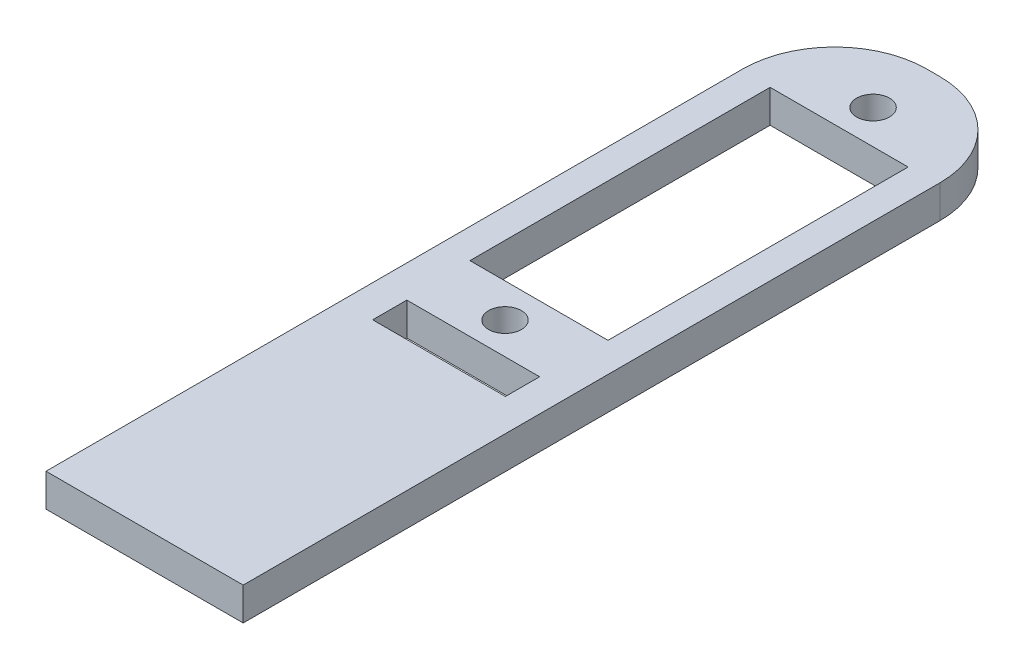
SolidWorks part; units mm, degrees
ref_plane "Front Plane" through (0, 0, 0) normal (0, 0, 1) x (1, 0, 0)
ref_plane "Top Plane" through (0, 0, 0) normal (0, 1, 0) x (1, 0, 0)
ref_plane "Right Plane" through (0, 0, 0) normal (1, 0, 0) x (0, 0, -1)
sketch "Sketch1" plane through (0, 0, 0) normal (0, 1, 0) x (1, 0, 0)
  line L0 (0, 29) -> (0, 0) construction
  line L1 (-9.525, 38.1) -> (9.525, 38.1)
  line L2 (-9.525, 38.1) -> (-9.525, -38.1)
  line L3 (-9.525, -38.1) -> (9.525, -38.1)
  line L4 (9.525, 38.1) -> (9.525, -38.1)
  line L5 (-6.6675, 29) -> (6.6675, 29)
  line L6 (-6.6675, 29) -> (-6.6675, 0)
  line L7 (-6.6675, 0) -> (6.6675, 0)
  line L8 (6.6675, 29) -> (6.6675, 0)
  line L9 (-6.6675, 14.5) -> (6.6675, 14.5) construction
  line L11 (-6.4135, -6.35) -> (6.4135, -6.35)
  line L12 (-6.4135, -6.35) -> (-6.4135, -9.652)
  line L13 (-6.4135, -9.652) -> (6.4135, -9.652)
  line L14 (6.4135, -6.35) -> (6.4135, -9.652)
  circle A0 centre (0, 32.28) radius 1.5875
  circle A1 centre (0, -3.28) radius 1.5875
  point P4 (0, 38.1)
  point P5 (9.525, 0)
  point P27 (0, -9.652)
  dimension "D5" = 3.175
  dimension "D1" = 19.05
  dimension "D2" = 76.2
  dimension "D3" = 13.335
  dimension "D4" = 29
  dimension "D6" = 17.78
  dimension "D7" = 0
  dimension "D8" = 3.302
  dimension "D9" = 12.827
  dimension "D10" = 6.35
extrude "Boss-Extrude1" add sketch "Sketch1" along normal blind 3.175
fillet "Fillet1" radius 8.89 1 edges at (9.525, 1.5875, -38.1)
fillet "Fillet2" radius 8.89 1 edges at (-9.525, 1.5875, -38.1)
